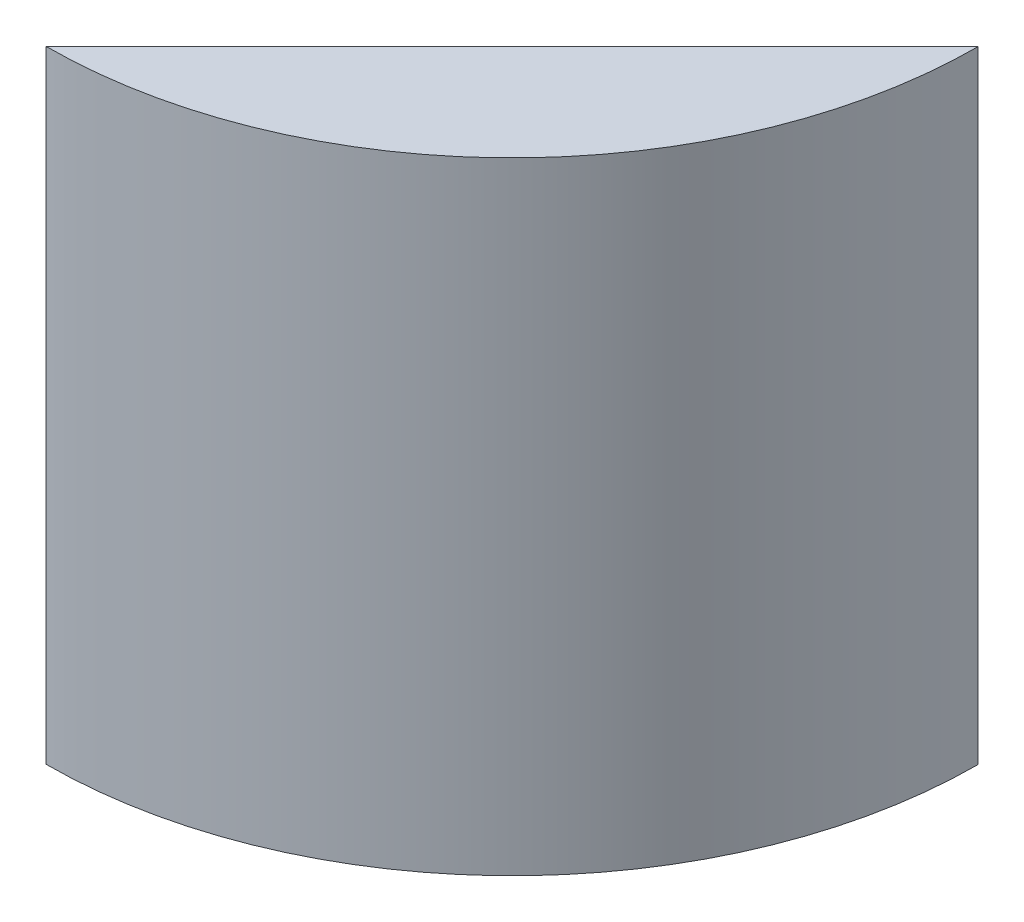
SolidWorks part; units mm, degrees
ref_plane "Front Plane" through (0, 0, 0) normal (0, 0, 1) x (1, 0, 0)
ref_plane "Top Plane" through (0, 0, 0) normal (0, 1, 0) x (1, 0, 0)
ref_plane "Right Plane" through (0, 0, 0) normal (1, 0, 0) x (0, 0, -1)
sketch "Sketch1" plane through (0, 0, 0) normal (0, 1, 0) x (1, 0, 0)
  circle A0 centre (0, 0) radius 85.725
extrude "Boss-Extrude1" add sketch "Sketch1" along normal blind 114.3
sketch "Sketch2" plane through (0, 114.3, 0) normal (0, 1, 0) x (1, 0, 0)
  line L0 (85.7249, -0.1067) -> (0, -85.725)
  line L1 (0, -85.725) -> (-45.6275, -96.7194)
  line L6 (-45.6275, -96.7194) -> (-137.4289, 46.1739)
  line L7 (-137.4289, 46.1739) -> (19.1253, 101.9105)
  line L8 (19.1253, 101.9105) -> (109.8339, 30.6005)
  line L9 (109.8339, 30.6005) -> (85.7249, -0.1067)
  circle A0 centre (0, 0) radius 85.725 construction
extrude "Cut-Extrude1" cut sketch "Sketch2" against normal blind 152.4
sketch "Sketch3" plane through (42.8625, 0, 42.9158) normal (-0.7067, 0, -0.7075) x (-0.7075, 0, 0.7067)
  line L0 (60.579, 0) -> (-60.579, 0) construction
  line L1 (-60.579, 0) -> (-60.579, 114.3) construction
  circle A0 centre (-37.719, 87.122) radius 2.7781
  circle A1 centre (-14.859, 87.122) radius 2.7781
  circle A2 centre (-37.719, 29.21) radius 2.7781
  circle A3 centre (-14.859, 29.21) radius 2.7781
  dimension "D1" = 29.21
  dimension "D2" = 57.912
  dimension "D3" = 22.86
  dimension "D4" = 22.86
  dimension "D5" = 57.912
  dimension "D6" = 22.86
extrude "Cut-Extrude2" cut sketch "Sketch3" against normal blind 12.7
sketch "Sketch4" plane through (0, 0, 0) normal (0, -1, 0) x (-1, 0, 0)
  line L0 (-42.8625, -42.9158) -> (-60.579, -60.6544) construction
  line L1 (0, -85.725) -> (-85.7249, -0.1067) construction
  arc A0 (-85.7249, -0.1067) -> (0, -85.725) centre (0, 0) ccw construction
  circle A1 centre (-51.7207, -51.7851) radius 6.985
  dimension "D1" = 13.97
extrude "Cut-Extrude3" cut sketch "Sketch4" against normal blind 6.096
